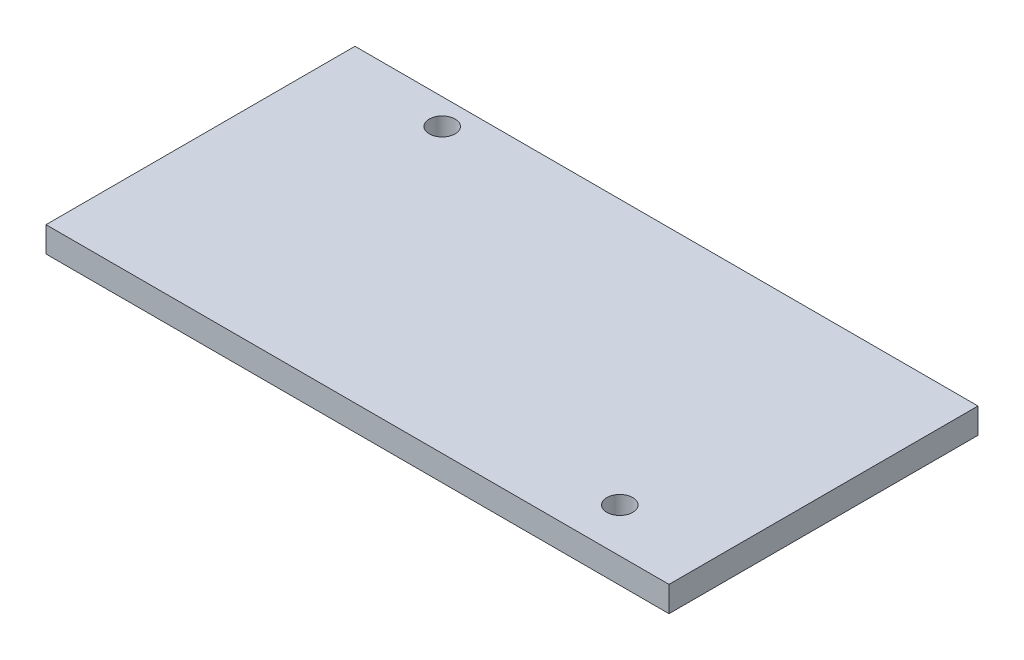
SolidWorks part; units mm, degrees
ref_plane "Front" through (0, 0, 0) normal (0, 0, 1) x (1, 0, 0)
ref_plane "Top" through (0, 0, 0) normal (0, 1, 0) x (1, 0, 0)
ref_plane "Right" through (0, 0, 0) normal (1, 0, 0) x (0, 0, -1)
sketch "Sketch1" plane through (0, 0, 0) normal (0, 1, 0) x (1, 0, 0)
  line L1 (0, 0) -> (49, 0)
  line L2 (0, 0) -> (0, -24.3)
  line L3 (0, -24.3) -> (49, -24.3)
  line L4 (49, 0) -> (49, -24.3)
  dimension "D1" = 24.3
  dimension "D2" = 49
extrude "Boss-Extrude1" add sketch "Sketch1" along normal blind 2
sketch "Sketch2" plane through (0, 2, 0) normal (0, 1, 0) x (1, 0, 0)
  line L0 (0, 0) -> (0, -24.3) construction
  line L1 (49, 0) -> (0, 0) construction
  line L2 (0, 0) -> (0, -24.3) construction
  circle A0 centre (8.89, -2.032) radius 1.015
  circle A1 centre (41.656, -20.828) radius 1.015
  dimension "D1" = 2.03
  dimension "D2" = 2.03
  dimension "D3" = 8.89
  dimension "D4" = 2.032
  dimension "D5" = 41.656
  dimension "D6" = 20.828
extrude "Cut-Extrude1" cut sketch "Sketch2" against normal through all
